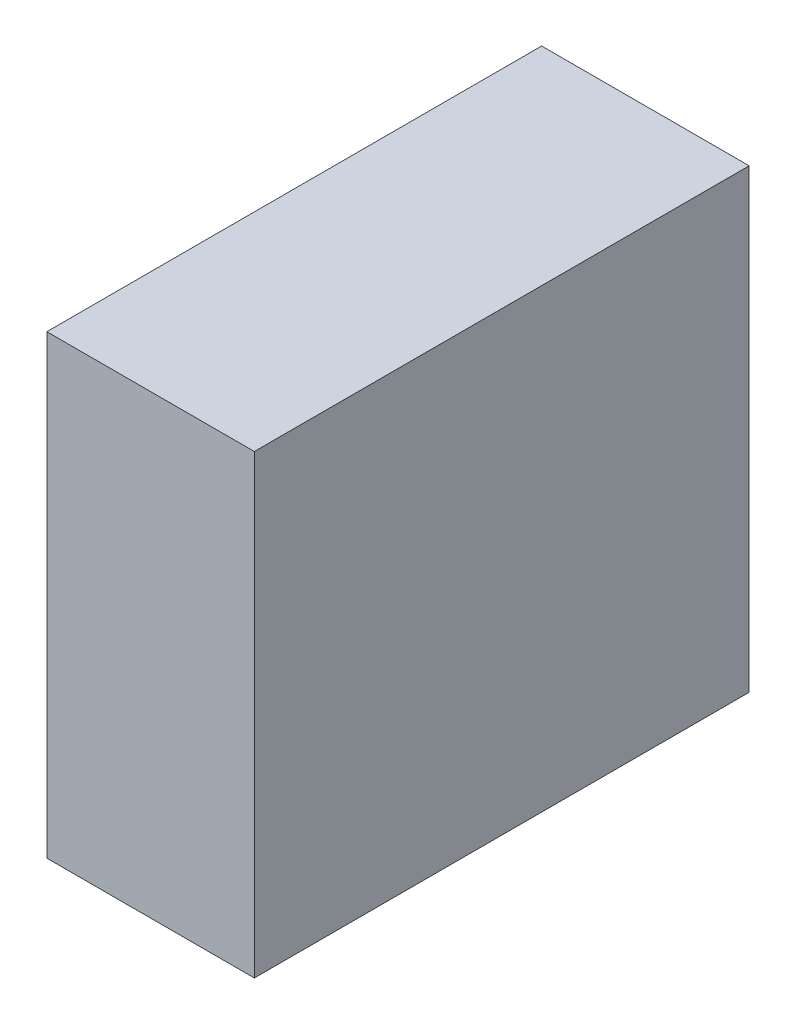
SolidWorks part; units mm, degrees
ref_plane "Front Plane" through (0, 0, 0) normal (0, 0, 1) x (1, 0, 0)
ref_plane "Top Plane" through (0, 0, 0) normal (0, 1, 0) x (1, 0, 0)
ref_plane "Right Plane" through (0, 0, 0) normal (1, 0, 0) x (0, 0, -1)
sketch "Sketch1" plane through (0, 0, 0) normal (0, 1, 0) x (1, 0, 0)
  line L1 (0, 0) -> (75.946, 0)
  line L2 (0, 0) -> (0, 181.102)
  line L3 (0, 181.102) -> (75.946, 181.102)
  line L4 (75.946, 0) -> (75.946, 181.102)
  dimension "D1" = 181.102
  dimension "D2" = 75.946
extrude "Boss-Extrude1" add sketch "Sketch1" along normal blind 166.878
